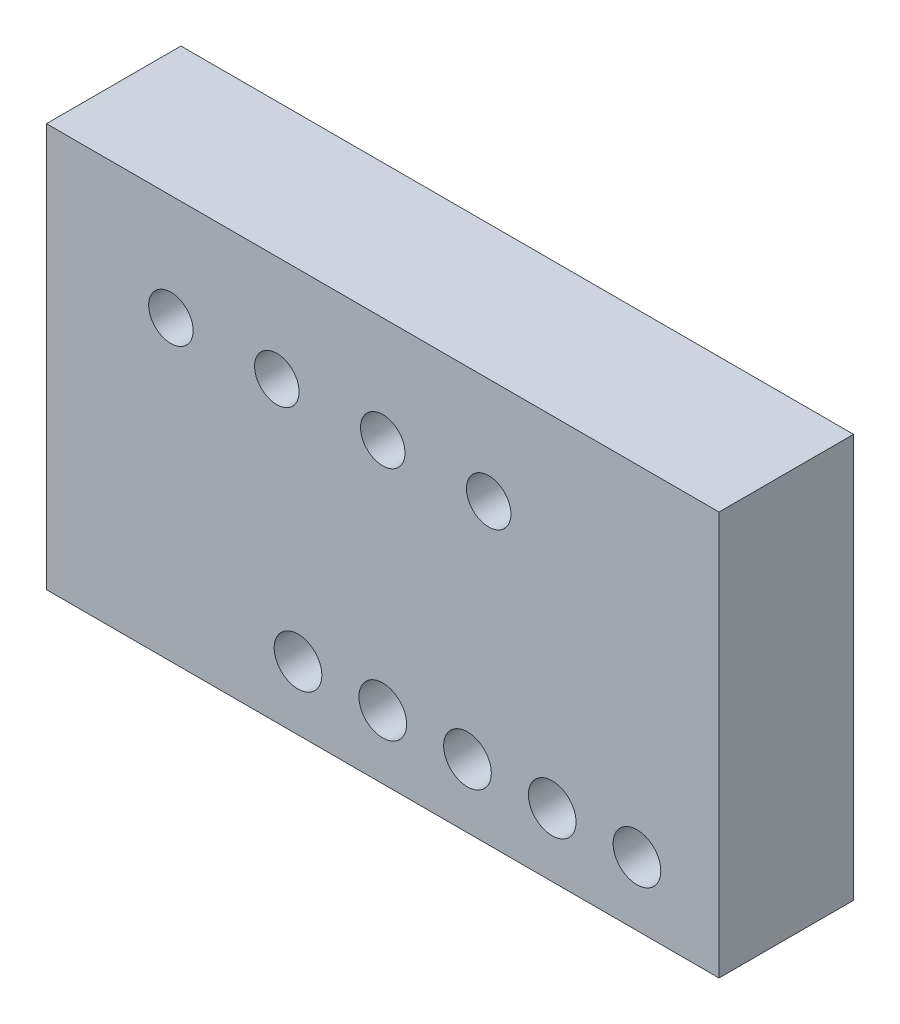
SolidWorks part; units mm, degrees
material "6061 Alloy"
ref_plane "Front Plane" through (0, 0, 0) normal (0, 0, 1) x (1, 0, 0)
ref_plane "Top Plane" through (0, 0, 0) normal (0, 1, 0) x (1, 0, 0)
ref_plane "Right Plane" through (0, 0, 0) normal (1, 0, 0) x (0, 0, -1)
sketch "Sketch1" plane through (0, 0, 0) normal (0, 0, 1) x (1, 0, 0)
  line L1 (31.75, -19.05) -> (-31.75, -19.05)
  line L2 (31.75, -19.05) -> (31.75, 19.05)
  line L3 (31.75, 19.05) -> (-31.75, 19.05)
  line L4 (-31.75, -19.05) -> (-31.75, 19.05)
  line L5 (31.75, -19.05) -> (-31.75, 19.05) construction
  line L6 (31.75, 19.05) -> (-31.75, -19.05) construction
  point P0 (0, 0)
  point P6 (0, -13.05)
  point P7 (-8, -13.05)
  point P8 (8, -13.05)
  point P9 (16, -13.05)
  point P10 (24, -13.05)
  point P11 (-10, 9.05)
  point P12 (0, 9.05)
  point P13 (10, 9.05)
  point P14 (-20, 9.05)
  dimension "D1" = 38.1
  dimension "D2" = 63.5
  dimension "D3" = 8
  dimension "D4" = 8
  dimension "D5" = 8
  dimension "D6" = 8
  dimension "D7" = 6
  dimension "D8" = 10
  dimension "D9" = 10
  dimension "D10" = 10
  dimension "D11" = 10
extrude "Boss-Extrude1" add sketch "Sketch1" along normal blind 12.7
hole_wizard "M4 Clearance Hole1" positions "Sketch2" profile "Sketch3" hole size "M4" standard "ANSI Metric" end condition through all
sketch "Sketch2" plane through (0, 0, 12.7) normal (0, 0, 1) x (1, 0, 0)
  point P0 (-8, -13.05)
  point P3 (0, -13.05)
  point P6 (8, -13.05)
  point P9 (16, -13.05)
  point P12 (24, -13.05)
sketch "Sketch3" plane through (-8, -13.05, 12.7) normal (1, 0, 0) x (0, -1, 0)
  line L0 (0, 0) -> (0, 12.7)
  line L1 (0, 12.7) -> (2.25, 12.7)
  line L2 (2.25, 12.7) -> (2.25, 0)
  line L5 (2.25, 0) -> (0, 0)
  line L11 (0, -6.35) -> (0, 107.95) construction
  dimension "Thru Hole Dia." = 4.5
  dimension "Thru Hole Depth" = 12.7
hole_wizard "M5x0.8 Tapped Hole1" positions "Sketch4" profile "Sketch5" tap size "M5x0.8" standard "ANSI Metric" end condition through all
sketch "Sketch4" plane through (0, 0, 12.7) normal (0, 0, 1) x (1, 0, 0)
  point P0 (-20, 9.05)
  point P3 (-10, 9.05)
  point P6 (0, 9.05)
  point P9 (10, 9.05)
sketch "Sketch5" plane through (-20, 9.05, 12.7) normal (1, 0, 0) x (0, -1, 0)
  line L0 (0, 0) -> (0, 12.7)
  line L1 (0, 12.7) -> (2.1, 12.7)
  line L2 (2.1, 12.7) -> (2.1, 0)
  line L5 (2.1, 0) -> (0, 0)
  line L11 (0, -6.35) -> (0, 107.95) construction
  dimension "Thru Tap Drill Dia." = 4.2
  dimension "Thru Tap Drill Depth" = 12.7
